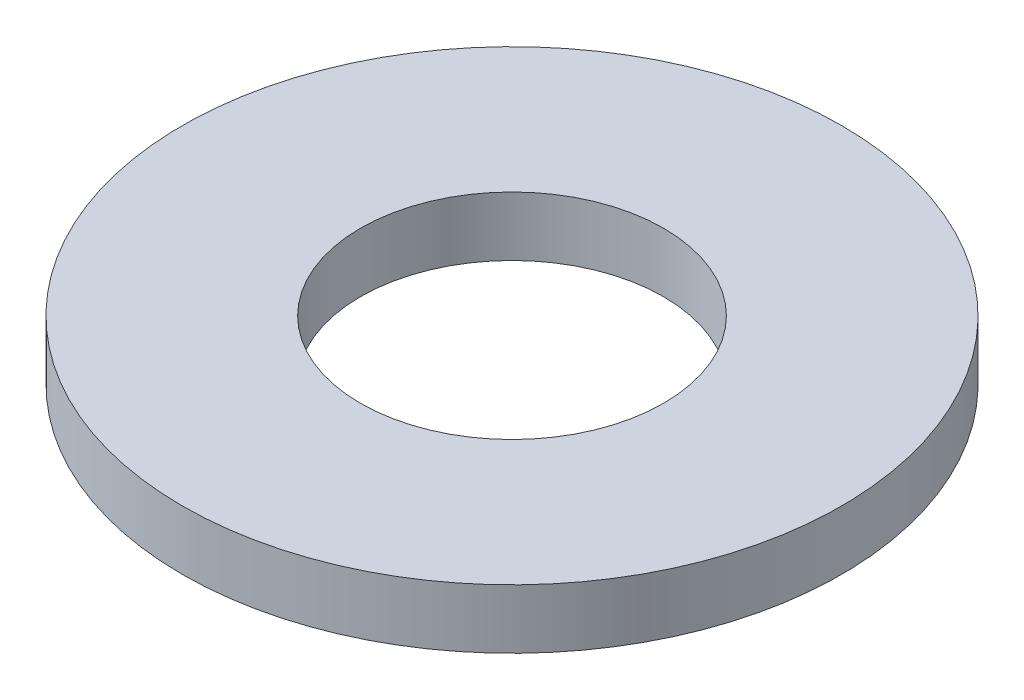
SolidWorks part; units mm, degrees
material "Plain Carbon Steel"
ref_plane "Front Plane" through (0, 0, 0) normal (0, 0, 1) x (1, 0, 0)
ref_plane "Top Plane" through (0, 0, 0) normal (0, 1, 0) x (1, 0, 0)
ref_plane "Right Plane" through (0, 0, 0) normal (1, 0, 0) x (0, 0, -1)
sketch "Sketch1" plane through (0, 0, 0) normal (0, 1, 0) x (1, 0, 0)
  circle A0 centre (0, 0) radius 12.5
  circle A1 centre (0, 0) radius 5.75
  dimension "D1" = 25
  dimension "D2" = 11.5
extrude "Boss-Extrude1" add sketch "Sketch1" along normal mid plane 2.25
